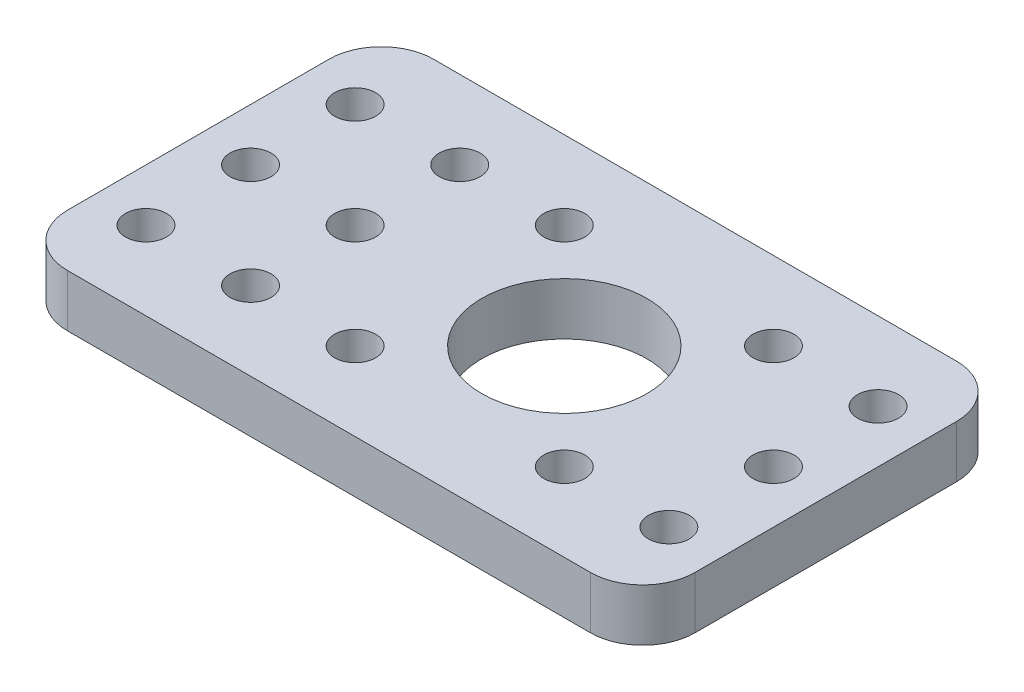
SolidWorks part; units mm, degrees
material "6061-T6 (SS)"
ref_plane "Front Plane" through (0, 0, 0) normal (0, 0, 1) x (1, 0, 0)
ref_plane "Top Plane" through (0, 0, 0) normal (0, 1, 0) x (1, 0, 0)
ref_plane "Right Plane" through (0, 0, 0) normal (1, 0, 0) x (0, 0, -1)
sketch "Sketch1" plane through (0, 0, 0) normal (0, 1, 0) x (1, 0, 0)
  line L1 (0, 0) -> (76.2, 0)
  line L2 (0, 0) -> (0, 44.45)
  line L3 (0, 44.45) -> (76.2, 44.45)
  line L4 (76.2, 0) -> (76.2, 44.45)
  dimension "D1" = 76.2
  dimension "D2" = 44.45
extrude "Boss-Extrude1" add sketch "Sketch1" along normal blind 6.35
fillet "Fillet1" radius 6.35 4 edges at (0, 3.175, -44.45) (76.2, 3.175, -44.45) (0, 3.175, 0) (76.2, 3.175, 0)
sketch "Sketch2" plane through (0, 6.35, 0) normal (0, 1, 0) x (1, 0, 0)
  line L1 (6.35, 0) -> (69.85, 0) construction
  line L3 (76.2, 6.35) -> (76.2, 38.1) construction
  circle A0 centre (31.75, 34.925) radius 2.4892 construction
  circle A1 centre (6.35, 34.925) radius 2.4892 construction
  circle A2 centre (19.05, 34.925) radius 2.4892 construction
  circle A3 centre (19.05, 22.225) radius 2.4892 construction
  circle A4 centre (6.35, 22.225) radius 2.4892 construction
  circle A5 centre (6.35, 9.525) radius 2.4892 construction
  circle A6 centre (19.05, 9.525) radius 2.4892 construction
  circle A7 centre (31.75, 9.525) radius 2.4892 construction
  circle A8 centre (57.15, 9.525) radius 2.4892 construction
  circle A9 centre (69.85, 9.525) radius 2.4892 construction
  circle A10 centre (69.85, 22.225) radius 2.4892 construction
  circle A11 centre (69.85, 34.925) radius 2.4892 construction
  circle A12 centre (57.15, 34.925) radius 2.4892 construction
  circle A14 centre (31.75, 34.925) radius 2.4892
  circle A15 centre (6.35, 34.925) radius 2.4892
  circle A16 centre (19.05, 34.925) radius 2.4892
  circle A17 centre (19.05, 22.225) radius 2.4892
  circle A18 centre (6.35, 22.225) radius 2.4892
  circle A19 centre (6.35, 9.525) radius 2.4892
  circle A20 centre (19.05, 9.525) radius 2.4892
  circle A21 centre (31.75, 9.525) radius 2.4892
  circle A22 centre (57.15, 9.525) radius 2.4892
  circle A23 centre (69.85, 9.525) radius 2.4892
  circle A24 centre (69.85, 22.225) radius 2.4892
  circle A25 centre (69.85, 34.925) radius 2.4892
  circle A26 centre (57.15, 34.925) radius 2.4892
  circle A27 centre (44.45, 22.225) radius 10.0254
  dimension "D3" = 20.0508
  dimension "D1" = 22.225
  dimension "D2" = 31.75
extrude "Cut-Extrude1" cut sketch "Sketch2" against normal through all
equation "\"D3@Sketch2\"=20mm+0.002in"
